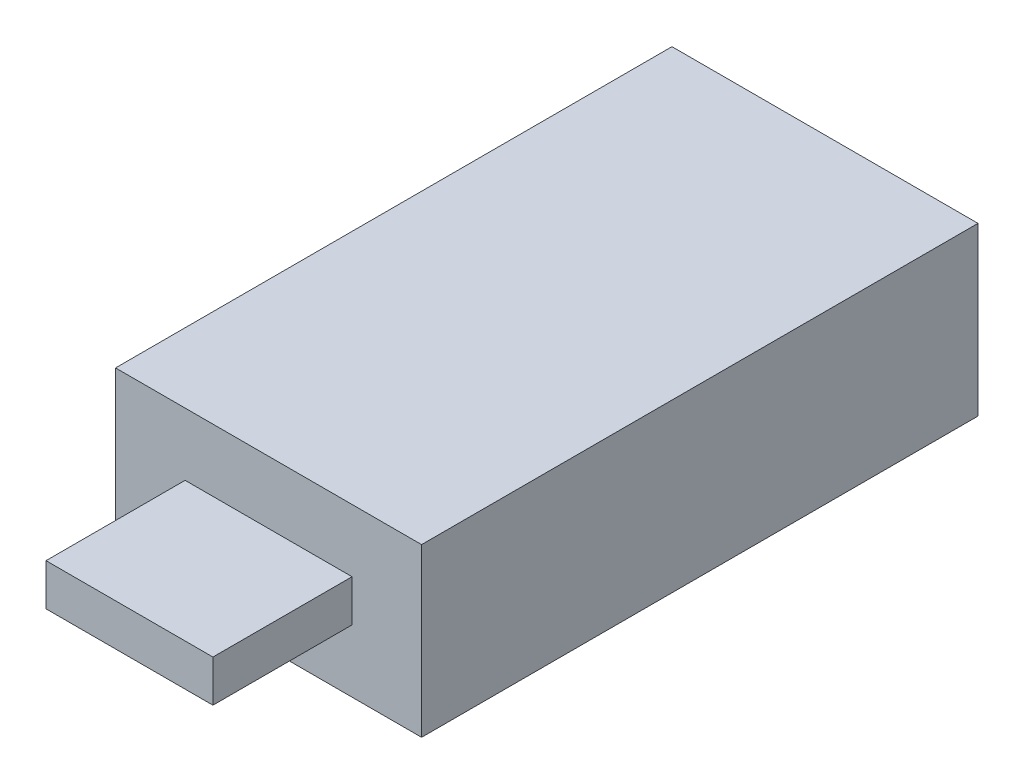
SolidWorks part; units mm, degrees
ref_plane "Front Plane" through (0, 0, 0) normal (0, 0, 1) x (1, 0, 0)
ref_plane "Top Plane" through (0, 0, 0) normal (0, 1, 0) x (1, 0, 0)
ref_plane "Right Plane" through (0, 0, 0) normal (1, 0, 0) x (0, 0, -1)
sketch "Sketch1" plane through (0, 0, 0) normal (0, 0, 1) x (1, 0, 0)
  line L1 (-11, 6) -> (11, 6)
  line L2 (-11, 6) -> (-11, -6)
  line L3 (-11, -6) -> (11, -6)
  line L4 (11, 6) -> (11, -6)
  line L5 (-11, 6) -> (11, -6) construction
  line L6 (-11, -6) -> (11, 6) construction
  point P0 (0, 0)
  dimension "D1" = 22
  dimension "D2" = 12
extrude "Boss-Extrude1" add sketch "Sketch1" along normal blind 40
sketch "Sketch2" plane through (0, 0, 40) normal (0, 0, 1) x (1, 0, 0)
  line L1 (-6, 1.5) -> (6, 1.5)
  line L2 (-6, 1.5) -> (-6, -1.5)
  line L3 (-6, -1.5) -> (6, -1.5)
  line L4 (6, 1.5) -> (6, -1.5)
  line L5 (-6, 1.5) -> (6, -1.5) construction
  line L6 (-6, -1.5) -> (6, 1.5) construction
  point P0 (0, 0)
  dimension "D1" = 12
  dimension "D2" = 3
extrude "Boss-Extrude2" add sketch "Sketch2" along normal blind 10
